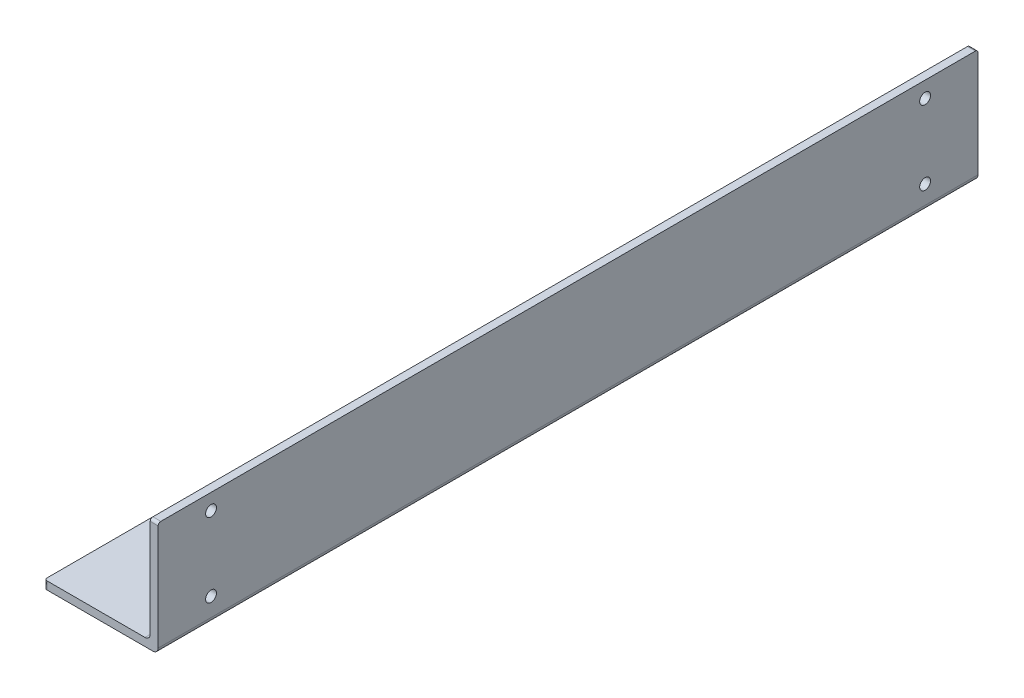
SolidWorks part; units mm, degrees
ref_plane "前视基准面" through (0, 0, 0) normal (0, 0, 1) x (1, 0, 0)
ref_plane "上视基准面" through (0, 0, 0) normal (0, 1, 0) x (1, 0, 0)
ref_plane "右视基准面" through (0, 0, 0) normal (1, 0, 0) x (0, 0, -1)
other "Configuration Table"
sketch "草图1" plane through (0, 0, 0) normal (1, 0, 0) x (0, 0, -1)
  line L0 (0, 0) -> (310, 0)
  line L1 (0, 0) -> (0, 43)
  line L2 (0, 43) -> (310, 43)
  line L3 (310, 43) -> (310, 0)
  dimension "D1" = 310
  dimension "D2" = 43
extrude "凸台-拉伸1" add sketch "草图1" along normal blind 3
sketch "草图2" plane through (0, 0, 0) normal (0, 1, 0) x (1, 0, 0)
  line L0 (0, 0) -> (-40, 0)
  line L1 (0, 0) -> (0, 310)
  line L2 (0, 310) -> (-40, 310)
  line L3 (-40, 310) -> (-40, 0)
  dimension "D1" = 40
extrude "凸台-拉伸2" add sketch "草图2" along normal blind 3
fillet "圆角1" radius 2 1 edges at (3, 0, -155)
fillet "圆角2" radius 2 1 edges at (0, 3, -155)
fillet "圆角3" radius 1 4 edges at (-40, 1.5, 0) (-40, 1.5, -310) (1.5, 43, -310) (1.5, 43, 0)
ref_plane "基准面1" through (0, 0, -155) normal (0, 0, 1) x (1, 0, 0)
sketch "草图3" plane through (3, 0, 0) normal (1, 0, 0) x (0, 0, -1)
  line L0 (0, 42) -> (0, 2) construction
  line L1 (309, 43) -> (1, 43) construction
  line L2 (155, 23.1) -> (155, -23.1) construction
  circle A0 centre (20, 37) radius 2.05
  circle A1 centre (20, 9) radius 2.05
  circle A2 centre (290, 9) radius 2.05
  circle A3 centre (290, 37) radius 2.05
  dimension "D1" = 4.1
  dimension "D2" = 4.1
  dimension "D3" = 20
  dimension "D4" = 20
  dimension "D5" = 28
  dimension "D6" = 6
extrude "切除-拉伸1" cut sketch "草图3" against normal through all
